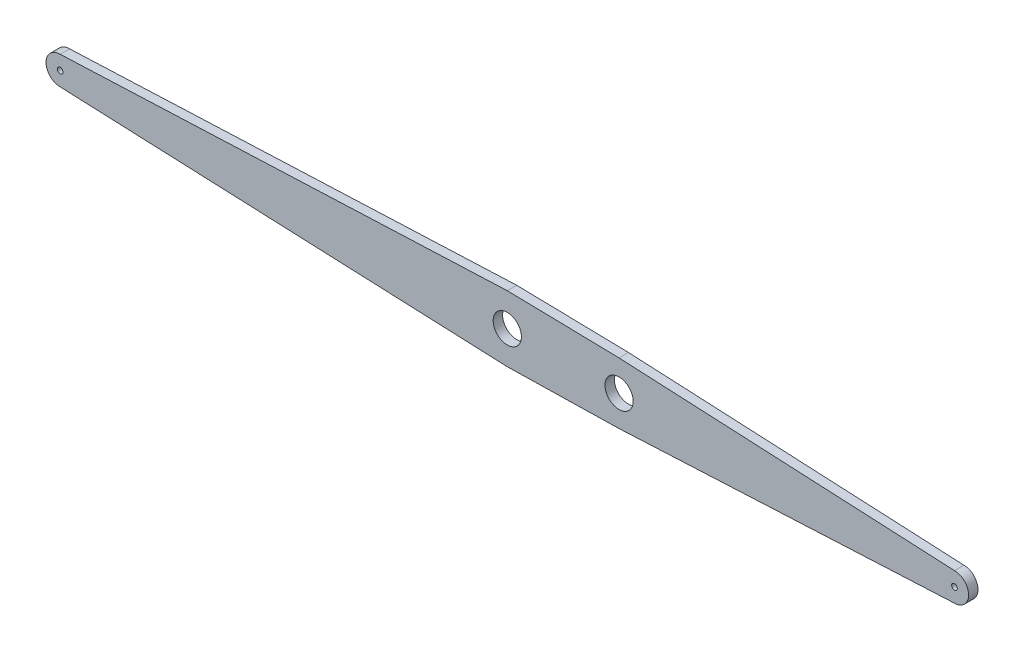
SolidWorks part; units mm, degrees
ref_plane "Ebene vorne" through (0, 0, 0) normal (0, 0, 1) x (1, 0, 0)
ref_plane "Ebene oben" through (0, 0, 0) normal (0, 1, 0) x (1, 0, 0)
ref_plane "Ebene rechts" through (0, 0, 0) normal (1, 0, 0) x (0, 0, -1)
sketch "Skizze1" plane through (0, 0, 0) normal (0, 0, 1) x (1, 0, 0)
  line L0 (0, 0) -> (-1900, 0) construction
  line L1 (-950, -70) -> (-950, 70) construction
  line L2 (-712.5, -65) -> (-712.5, 65) construction
  line L3 (-950, 70) -> (-712.5, 65)
  line L4 (-712.5, 65) -> (0, 30)
  line L5 (0, 0) -> (89.2748, 0) construction
  line L6 (-1900, 0) -> (-1989.2748, 0) construction
  line L7 (-1900, -30) -> (-950, -70)
  line L8 (-1900, 30) -> (-950, 70)
  line L11 (-712.5, -65) -> (0, -30)
  line L12 (-950, -70) -> (-712.5, -65)
  circle A0 centre (-950, 0) radius 30
  arc A1 (0, -30) -> (0, 30) centre (0, 0) ccw
  circle A2 centre (-712.5, 0) radius 30
  circle A3 centre (-1900, 0) radius 6
  arc A4 (-1900, -30) -> (-1900, 30) centre (-1900, 0) cw
  circle A5 centre (0, 0) radius 6
  dimension "D3" = 60
  dimension "D6" = 60
  dimension "D7" = 30
  dimension "D8" = 12
  dimension "D9" = 12
  dimension "D1" = 1900
  dimension "D2" = 140
  dimension "D4" = 237.5
  dimension "D5" = 130
extrude "Aufsatz-Linear austragen1" add sketch "Skizze1" along normal blind 20
